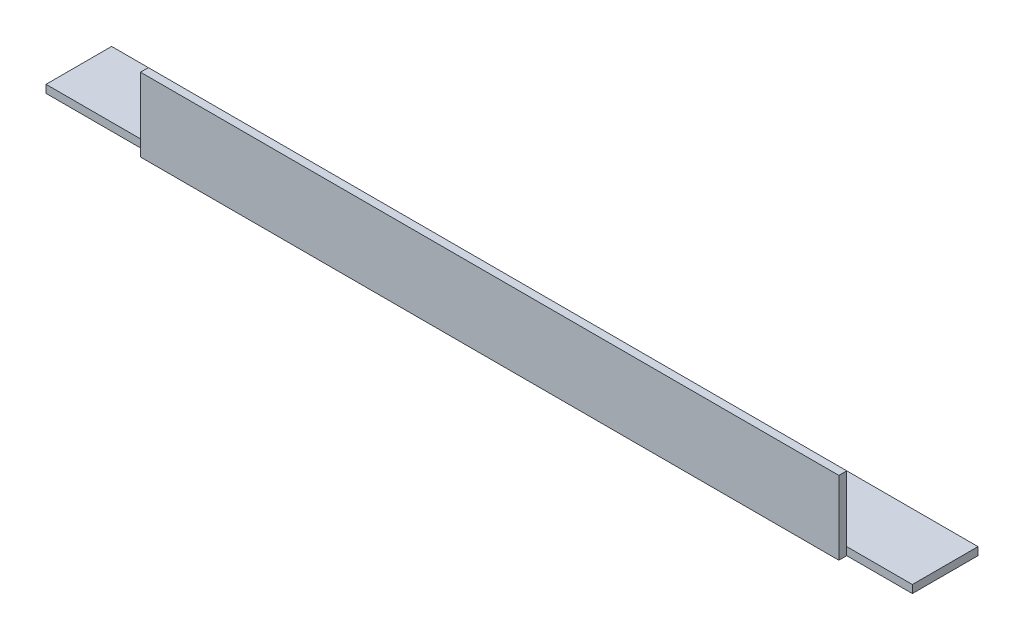
SolidWorks part; units mm, degrees
ref_plane "Спереди" through (0, 0, 0) normal (0, 0, 1) x (1, 0, 0)
ref_plane "Сверху" through (0, 0, 0) normal (0, 1, 0) x (1, 0, 0)
ref_plane "Справа" through (0, 0, 0) normal (1, 0, 0) x (0, 0, -1)
sketch "Эскиз1" plane through (0, 0, 0) normal (1, 0, 0) x (0, 0, -1)
  line L0 (0, 25) -> (0, 0)
  line L1 (0, 0) -> (25, 0)
extrude "Вытянуть-Тонкостенный1" add sketch "Эскиз1" along normal blind 330 thin
sketch "Эскиз2" plane through (0, -3, 0) normal (0, -1, 0) x (1, 0, 0)
  line L0 (330, 3) -> (330, -25) construction
  line L1 (0, 3) -> (39, 3)
  line L2 (0, 3) -> (0, 0)
  line L3 (0, 0) -> (39, 0)
  line L4 (39, 3) -> (39, 0)
  line L5 (330, 3) -> (305, 3)
  line L6 (330, 3) -> (330, 0)
  line L7 (330, 0) -> (305, 0)
  line L8 (305, 3) -> (305, 0)
  line L9 (330, 3) -> (0, 3) construction
extrude "Вырез-Вытянуть1" cut sketch "Эскиз2" against normal through all
